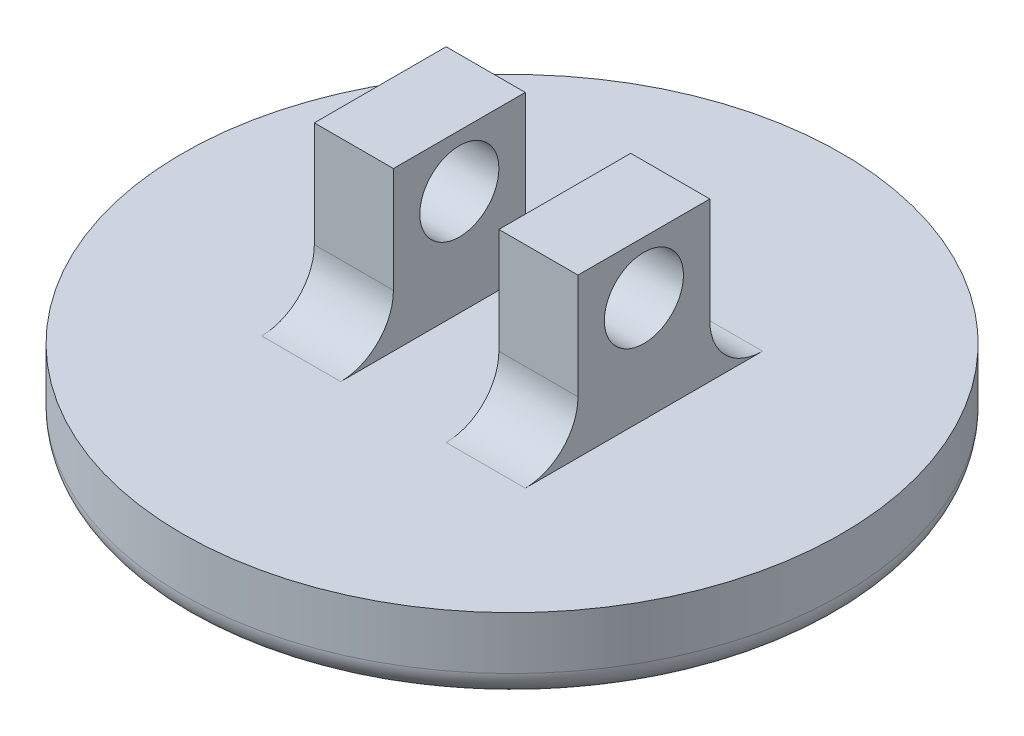
SolidWorks part; units mm, degrees
ref_plane "Front Plane" through (0, 0, 0) normal (0, 0, 1) x (1, 0, 0)
ref_plane "Top Plane" through (0, 0, 0) normal (0, 1, 0) x (1, 0, 0)
ref_plane "Right Plane" through (0, 0, 0) normal (1, 0, 0) x (0, 0, -1)
sketch "Sketch1" plane through (0, 0, 0) normal (0, 1, 0) x (1, 0, 0)
  circle A0 centre (0, 0) radius 12.5
  dimension "D1" = 25
extrude "Boss-Extrude1" add sketch "Sketch1" along normal blind 3
sketch "Sketch2" plane through (0, 3, 0) normal (0, 1, 0) x (1, 0, 0)
  line L0 (-5, 0) -> (5, 0) construction
  line L2 (-5, 2.5) -> (-2, 2.5)
  line L3 (-5, 2.5) -> (-5, -2.5)
  line L4 (-5, -2.5) -> (-2, -2.5)
  line L5 (-2, 2.5) -> (-2, -2.5)
  line L6 (-5, 2.5) -> (-2, -2.5) construction
  line L7 (-5, -2.5) -> (-2, 2.5) construction
  line L8 (2, 2.5) -> (5, 2.5)
  line L9 (2, 2.5) -> (2, -2.5)
  line L10 (2, -2.5) -> (5, -2.5)
  line L11 (5, 2.5) -> (5, -2.5)
  line L12 (2, 2.5) -> (5, -2.5) construction
  line L13 (2, -2.5) -> (5, 2.5) construction
  point P2 (0, 0)
  point P3 (-3.5, 0)
  point P9 (3.5, 0)
  point P14 (0, 0)
  point P15 (0, 0)
  dimension "D1" = 10
  dimension "D2" = 3
  dimension "D3" = 5
extrude "Boss-Extrude2" add sketch "Sketch2" along normal blind 6
sketch "Sketch3" plane through (5, 0, 0) normal (1, 0, 0) x (0, 0, -1)
  line L0 (0, 9) -> (0, 7) construction
  line L1 (-2.5, 9) -> (2.5, 9) construction
  circle A0 centre (0, 7) radius 1.5
  dimension "D1" = 3
  dimension "D2" = 2
extrude "Cut-Extrude1" cut sketch "Sketch3" against normal through all both and the other way through all
fillet "Fillet1" radius 2 4 edges at (-3.5, 3, 2.5) (-3.5, 3, -2.5) (3.5, 3, -2.5) (3.5, 3, 2.5)
fillet "Fillet2" radius 1 1 edges at (0, 0, 12.5)
